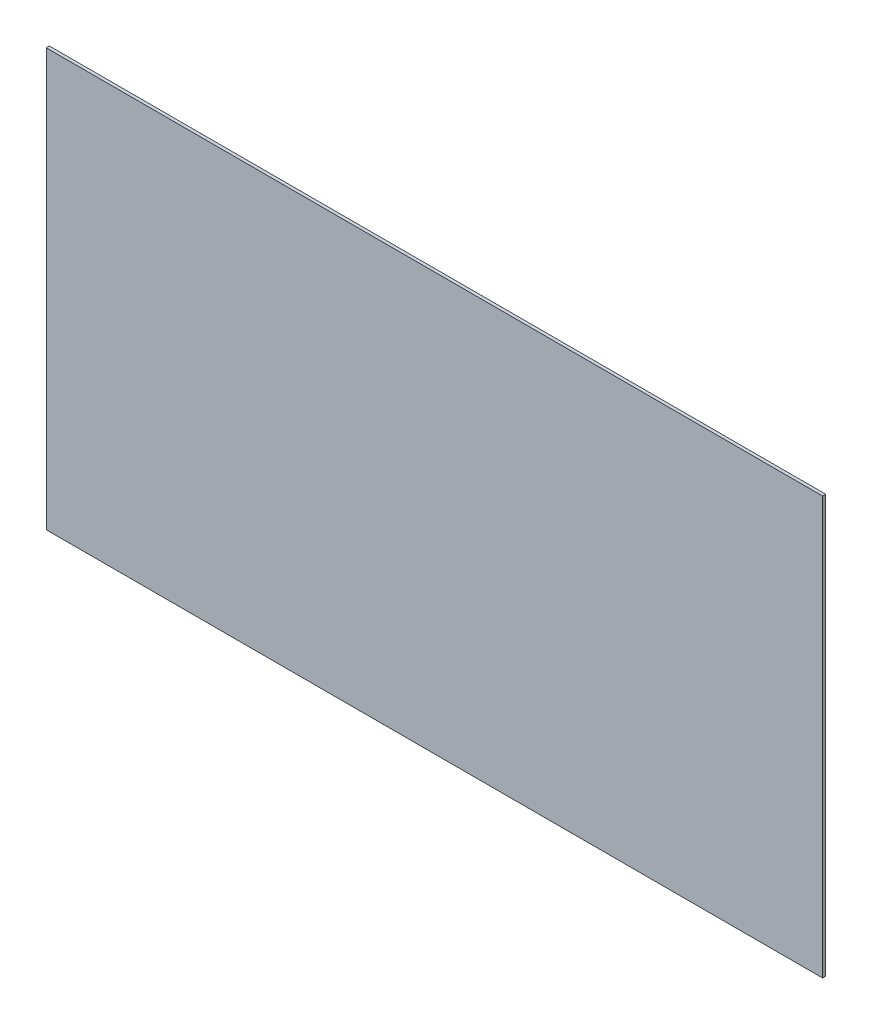
SolidWorks part; units mm, degrees
ref_plane "Front Plane" through (0, 0, 0) normal (0, 0, 1) x (1, 0, 0)
ref_plane "Top Plane" through (0, 0, 0) normal (0, 1, 0) x (1, 0, 0)
ref_plane "Right Plane" through (0, 0, 0) normal (1, 0, 0) x (0, 0, -1)
sketch "Sketch1" plane through (0, 0, 0) normal (0, 0, 1) x (1, 0, 0)
  line L1 (0, 0) -> (372, 0)
  line L2 (0, 0) -> (0, 200)
  line L3 (0, 200) -> (372, 200)
  line L4 (372, 0) -> (372, 200)
extrude "Extrude1" add sketch "Sketch1" along normal blind 1.5
